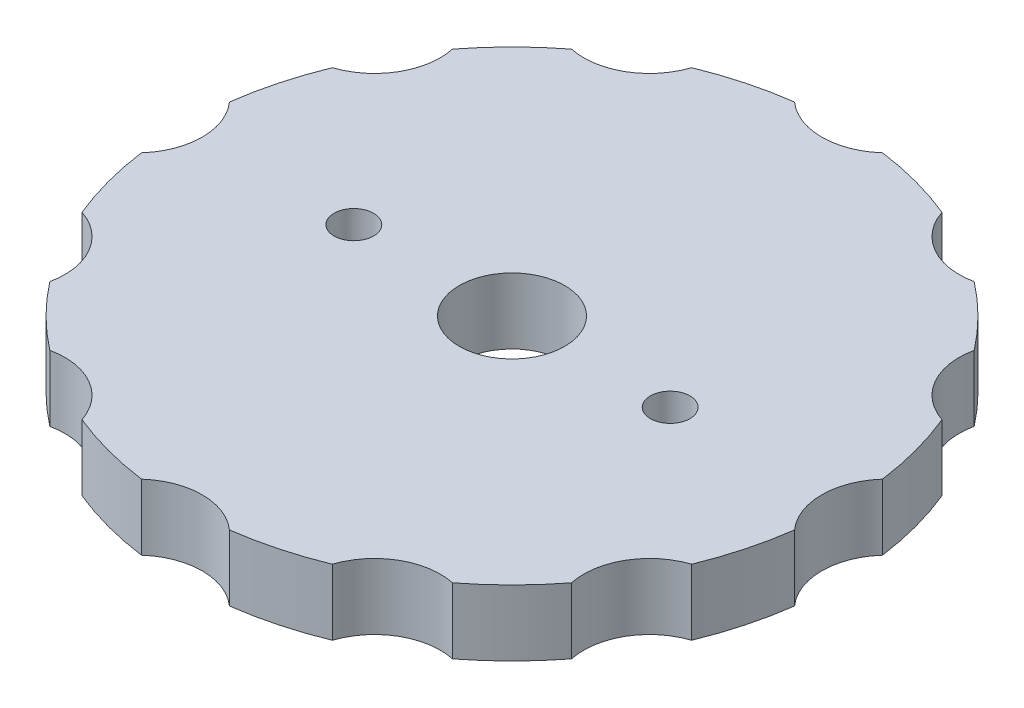
SolidWorks part; units mm, degrees
material "Brass"
ref_plane "Front Plane" through (0, 0, 0) normal (0, 0, 1) x (1, 0, 0)
ref_plane "Top Plane" through (0, 0, 0) normal (0, 1, 0) x (1, 0, 0)
ref_plane "Right Plane" through (0, 0, 0) normal (1, 0, 0) x (0, 0, -1)
sketch "Sketch1" plane through (0, 0, 0) normal (0, 1, 0) x (1, 0, 0)
  circle A0 centre (0, 0) radius 25
  dimension "D1" = 50
extrude "Boss-Extrude1" add sketch "Sketch1" along normal blind 5
sketch "Sketch2" plane through (0, 0, 0) normal (0, 1, 0) x (1, 0, 0)
  line L0 (0, 28.5) -> (0, 0) construction
  circle A0 centre (0, 28.5) radius 5
  circle A1 centre (0, 0) radius 25 construction
  point P6 (0, 25)
  dimension "D1" = 10
  dimension "D2" = 3.5
extrude "Cut-Extrude1" cut sketch "Sketch2" along normal through all
pattern_circular "CirPattern1" count 12 over 360 about axis through (0, 0, 0) along (0, 1, 0) of "Cut-Extrude1"
sketch "Sketch3" plane through (0, 0, 0) normal (0, 1, 0) x (1, 0, 0)
  circle A0 centre (0, 0) radius 4
  dimension "D1" = 8
extrude "Cut-Extrude2" cut sketch "Sketch3" along normal through all
sketch "Sketch4" plane through (0, 5, 0) normal (0, 1, 0) x (1, 0, 0)
  line L0 (0, 23.5) -> (0, -23.5) construction
  arc A0 (-3.3368, 24.7763) -> (3.3368, 24.7763) centre (0, 28.5) ccw construction
  arc A1 (3.3368, -24.7763) -> (-3.3368, -24.7763) centre (0, -28.5) ccw construction
  circle A2 centre (-12, 0) radius 1.5
  circle A3 centre (12, 0) radius 1.5
  dimension "D2" = 3
  dimension "D1" = 12
extrude "Cut-Extrude3" cut sketch "Sketch4" against normal through all
